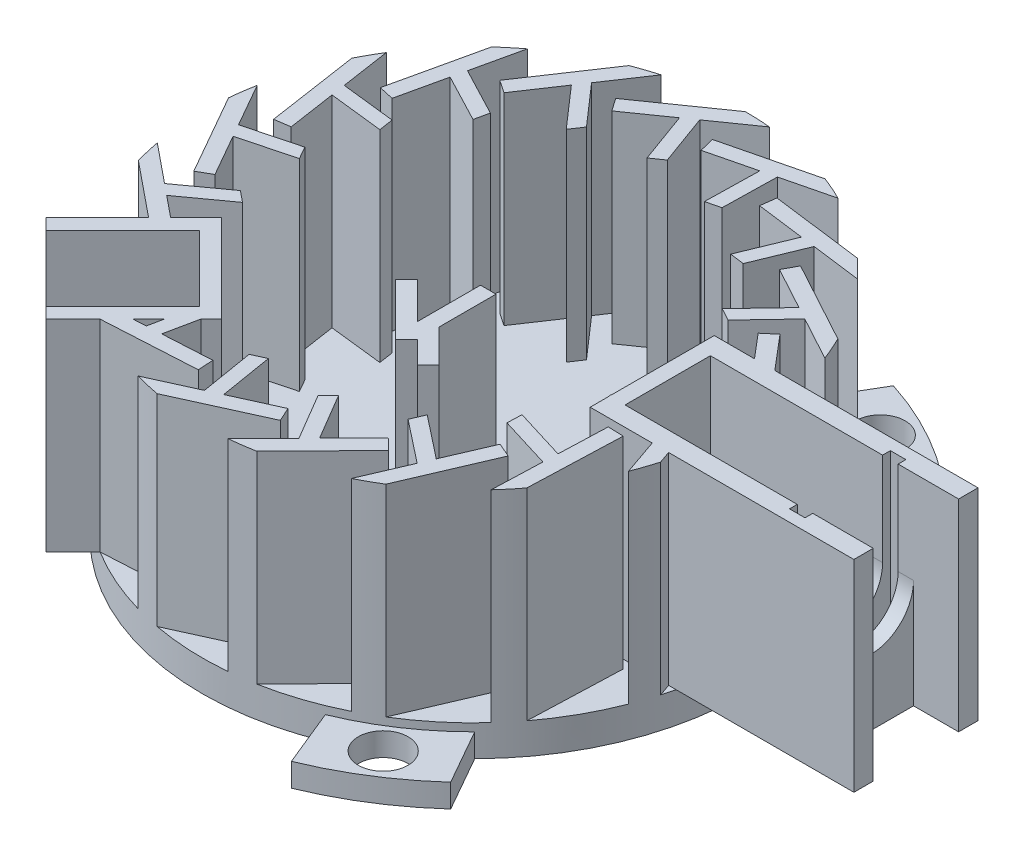
SolidWorks part; units mm, degrees
ref_plane "Front Plane" through (0, 0, 0) normal (0, 0, 1) x (1, 0, 0)
ref_plane "Top Plane" through (0, 0, 0) normal (0, 1, 0) x (1, 0, 0)
ref_plane "Right Plane" through (0, 0, 0) normal (1, 0, 0) x (0, 0, -1)
sketch "Sketch1" plane through (0, 0, 0) normal (0, 1, 0) x (1, 0, 0)
  circle A0 centre (0, 0) radius 17.5
  dimension "D1" = 35
extrude "Boss-Extrude1" add sketch "Sketch1" along normal blind 2
sketch "Sketch6" plane through (0, 2, 0) normal (0, 1, 0) x (1, 0, 0)
  line L1 (0, 17.5) -> (-4.9149, 14.0585)
  line L2 (-4.9149, 14.0585) -> (-4.3413, 13.2394)
  line L3 (-4.3413, 13.2394) -> (-1.7776, 15.0346)
  line L4 (-1.3536, 15.3315) -> (-0.3275, 12.5124) construction
  line L5 (-1.7776, 15.0346) -> (-0.5805, 11.7456)
  line L6 (-1.0084, 15.5731) -> (0.1886, 12.2842)
  line L7 (-0.5805, 11.7456) -> (0.1886, 12.2842)
  line L8 (-1.0084, 15.5731) -> (1.6342, 17.4235)
  line L9 (6.3217, 16.3183) -> (0.4955, 14.8847)
  line L10 (0.4955, 14.8847) -> (0.7344, 13.9136)
  line L11 (0.7344, 13.9136) -> (3.7736, 14.6614)
  line L12 (3.7736, 14.6614) -> (3.7017, 11.1622)
  line L13 (3.7017, 11.1622) -> (4.6135, 11.3865)
  line L14 (4.6853, 14.8858) -> (4.6135, 11.3865)
  line L15 (4.6853, 14.8858) -> (7.818, 15.6566)
  line L16 (11.7897, 12.9327) -> (5.839, 13.7005)
  line L17 (5.839, 13.7005) -> (5.711, 12.7088)
  line L18 (5.711, 12.7088) -> (8.8151, 12.3082)
  line L19 (8.8151, 12.3082) -> (7.484, 9.0712)
  line L20 (7.484, 9.0712) -> (8.4152, 8.951)
  line L21 (9.7463, 12.188) -> (8.4152, 8.951)
  line L22 (9.7463, 12.188) -> (12.9459, 11.7752)
  line L23 (15.6654, 7.8004) -> (10.3939, 10.6661)
  line L24 (10.3939, 10.6661) -> (9.9163, 9.7875)
  line L25 (9.9163, 9.7875) -> (12.666, 8.2927)
  line L26 (12.666, 8.2927) -> (10.2555, 5.7551)
  line L27 (10.2555, 5.7551) -> (11.0804, 5.3067)
  line L28 (13.491, 7.8442) -> (11.0804, 5.3067)
  line L29 (13.491, 7.8442) -> (16.3253, 6.3034)
  line L30 (17.4253, 1.6147) -> (13.5451, 6.1911)
  line L31 (13.5451, 6.1911) -> (12.7823, 5.5444)
  line L32 (12.7823, 5.5444) -> (14.8064, 3.1572)
  line L33 (14.8064, 3.1572) -> (11.642, 1.6618)
  line L34 (11.642, 1.6618) -> (12.2492, 0.9456)
  line L35 (15.4136, 2.441) -> (12.2492, 0.9456)
  line L36 (15.4136, 2.441) -> (17.5, -0.0196)
  line L37 (16.8319, -4.7891) -> (14.8669, 0.88)
  line L38 (14.8669, 0.88) -> (13.922, 0.5525)
  line L39 (13.922, 0.5525) -> (14.9471, -2.4047)
  line L40 (14.9471, -2.4047) -> (11.4561, -2.656)
  line L41 (11.4561, -2.656) -> (11.7636, -3.5432)
  line L42 (15.2546, -3.2919) -> (11.7636, -3.5432)
  line L43 (15.2546, -3.2919) -> (16.3112, -6.34)
  line L44 (13.9653, -10.5461) -> (14.1809, -4.55)
  line L45 (14.1809, -4.55) -> (13.1815, -4.5141)
  line L46 (13.1815, -4.5141) -> (13.0691, -7.6418)
  line L47 (13.0691, -7.6418) -> (9.723, -6.6151)
  line L48 (9.723, -6.6151) -> (9.6893, -7.5534)
  line L49 (13.0353, -8.5802) -> (9.6893, -7.5534)
  line L50 (13.0353, -8.5802) -> (12.9194, -11.8042)
  line L51 (9.2126, -14.8788) -> (11.5796, -9.3654)
  line L52 (11.5796, -9.3654) -> (10.6607, -8.9709)
  line L53 (10.6607, -8.9709) -> (9.426, -11.8469)
  line L54 (9.426, -11.8469) -> (6.6768, -9.6807)
  line L55 (6.6768, -9.6807) -> (6.3064, -10.5435)
  line L56 (9.0556, -12.7097) -> (6.3064, -10.5435)
  line L57 (9.0556, -12.7097) -> (7.7829, -15.6741)
  line L58 (3.2156, -17.202) -> (7.4145, -12.9161)
  line L59 (7.4145, -12.9161) -> (6.7001, -12.2162)
  line L60 (6.7001, -12.2162) -> (4.5099, -14.4519)
  line L61 (4.5099, -14.4519) -> (2.7289, -11.439)
  line L62 (2.7289, -11.439) -> (2.0718, -12.1097)
  line L63 (3.8528, -15.1227) -> (2.0718, -12.1097)
  line L64 (3.8528, -15.1227) -> (1.5952, -17.4271)
  line L65 (-3.2156, -17.202) -> (2.248, -14.7223)
  line L66 (2.248, -14.7223) -> (1.8347, -13.8117)
  line L67 (1.8347, -13.8117) -> (-1.0153, -15.1052)
  line L68 (-1.0153, -15.1052) -> (-1.5876, -11.6523)
  line L69 (-1.5876, -11.6523) -> (-2.4426, -12.0404)
  line L70 (-1.8703, -15.4933) -> (-2.4426, -12.0404)
  line L71 (-1.8703, -15.4933) -> (-4.808, -16.8266)
  line L72 (-9.2126, -14.8788) -> (-3.2221, -14.5402)
  line L73 (-3.2221, -14.5402) -> (-3.2786, -13.5418)
  line L74 (-3.2786, -13.5418) -> (-6.4033, -13.7184)
  line L75 (-6.4033, -13.7184) -> (-5.6897, -10.2919)
  line L76 (-5.6897, -10.2919) -> (-6.6272, -10.3449)
  line L77 (-7.3408, -13.7714) -> (-6.6272, -10.3449)
  line L78 (-7.3408, -13.7714) -> (-10.5618, -13.9535)
  line L79 (-13.9653, -10.5461) -> (-8.2571, -12.3943)
  line L80 (-8.2571, -12.3943) -> (-7.949, -11.443)
  line L81 (-7.949, -11.443) -> (-10.9266, -10.4789)
  line L82 (-10.9266, -10.4789) -> (-9.0234, -7.5416)
  line L83 (-9.0234, -7.5416) -> (-9.9167, -7.2523)
  line L84 (-11.8199, -10.1896) -> (-9.9167, -7.2523)
  line L85 (-11.8199, -10.1896) -> (-14.8891, -9.1959)
  line L86 (-16.8319, -4.7891) -> (-12.1768, -8.5746)
  line L87 (-12.1768, -8.5746) -> (-11.5459, -7.7987)
  line L88 (-11.5459, -7.7987) -> (-13.9742, -5.8241)
  line L89 (-13.9742, -5.8241) -> (-11.1384, -3.7727)
  line L90 (-11.1384, -3.7727) -> (-11.8669, -3.1803)
  line L91 (-14.7027, -5.2317) -> (-11.8669, -3.1803)
  line L92 (-14.7027, -5.2317) -> (-17.2056, -3.1963)
  line L93 (-17.4253, 1.6147) -> (-14.4521, -3.5968)
  line L94 (-14.4521, -3.5968) -> (-13.5835, -3.1012)
  line L95 (-13.5835, -3.1012) -> (-15.1344, -0.3828)
  line L96 (-15.1344, -0.3828) -> (-11.7491, 0.5057)
  line L97 (-11.7491, 0.5057) -> (-12.2144, 1.3213)
  line L98 (-15.5997, 0.4328) -> (-12.2144, 1.3213)
  line L99 (-15.5997, 0.4328) -> (-17.1984, 3.2349)
  line L100 (-15.6654, 7.8004) -> (-14.7755, 1.8668)
  line L101 (-14.7755, 1.8668) -> (-13.7865, 2.0151)
  line L102 (-13.7865, 2.0151) -> (-14.2507, 5.1103)
  line L103 (-14.2507, 5.1103) -> (-10.773, 4.7158)
  line L104 (-10.773, 4.7158) -> (-10.9123, 5.6444)
  line L105 (-14.39, 6.0388) -> (-10.9123, 5.6444)
  line L106 (-14.39, 6.0388) -> (-14.8685, 9.2292)
  line L107 (-11.7897, 12.9327) -> (-13.1033, 7.0782)
  line L108 (-13.1033, 7.0782) -> (-12.1276, 6.8593)
  line L109 (-12.1276, 6.8593) -> (-11.4424, 9.9131)
  line L110 (-11.4424, 9.9131) -> (-8.342, 8.289)
  line L111 (-8.342, 8.289) -> (-8.1364, 9.2052)
  line L112 (-11.2368, 10.8293) -> (-8.1364, 9.2052)
  line L113 (-11.2368, 10.8293) -> (-10.5304, 13.9771)
  line L114 (-6.3217, 16.3183) -> (-9.6616, 11.3337)
  line L115 (-9.6616, 11.3337) -> (-8.8308, 10.7771)
  line L116 (-8.8308, 10.7771) -> (-7.0886, 13.3772)
  line L117 (-7.0886, 13.3772) -> (-4.7843, 10.7428)
  line L118 (-4.7843, 10.7428) -> (-4.2617, 11.5228)
  line L119 (-6.566, 14.1572) -> (-4.2617, 11.5228)
  line L120 (-6.566, 14.1572) -> (-4.7702, 16.8373)
  circle A1 centre (0, 0) radius 17.5
  arc A2 (1.6342, 17.4235) -> (0, 17.5) centre (0, 0) ccw
  arc A3 (7.818, 15.6566) -> (6.3217, 16.3183) centre (0, 0) ccw
  arc A4 (12.9459, 11.7752) -> (11.7897, 12.9327) centre (0, 0) ccw
  arc A5 (16.3253, 6.3034) -> (15.6654, 7.8004) centre (0, 0) ccw
  arc A6 (17.5, -0.0196) -> (17.4253, 1.6147) centre (0, 0) ccw
  arc A7 (16.3112, -6.34) -> (16.8319, -4.7891) centre (0, 0) ccw
  arc A8 (12.9194, -11.8042) -> (13.9653, -10.5461) centre (0, 0) ccw
  arc A9 (7.7829, -15.6741) -> (9.2126, -14.8788) centre (0, 0) ccw
  arc A10 (1.5952, -17.4271) -> (3.2156, -17.202) centre (0, 0) ccw
  arc A11 (-4.808, -16.8266) -> (-3.2156, -17.202) centre (0, 0) ccw
  arc A12 (-10.5618, -13.9535) -> (-9.2126, -14.8788) centre (0, 0) ccw
  arc A13 (-14.8891, -9.1959) -> (-13.9653, -10.5461) centre (0, 0) ccw
  arc A14 (-17.2056, -3.1963) -> (-16.8319, -4.7891) centre (0, 0) ccw
  arc A15 (-17.1984, 3.2349) -> (-17.4253, 1.6147) centre (0, 0) ccw
  arc A16 (-14.8685, 9.2292) -> (-15.6654, 7.8004) centre (0, 0) ccw
  arc A17 (-10.5304, 13.9771) -> (-11.7897, 12.9327) centre (0, 0) ccw
  arc A18 (-4.7702, 16.8373) -> (-6.3217, 16.3183) centre (0, 0) ccw
  point P135 (0, 0)
  point P143 (0, 0)
  dimension "D2" = 6
  dimension "D3" = 3.5
  dimension "D4" = 1
  dimension "D5" = 3
  dimension "D6" = 75
  dimension "D7" = 0.5
  dimension "D8" = 3.5
  dimension "D9" = 17
  dimension "D1" = 0
extrude "Boss-Extrude2" add sketch "Sketch6" along normal blind 13
sketch "Sketch7" plane through (0, 2, 0) normal (0, 1, 0) x (1, 0, 0)
  line L0 (0, 0) -> (28.1783, 0) construction
  line L1 (11.5, 4) -> (28.5, 4)
  line L2 (11.5, 4) -> (11.5, -4)
  line L3 (11.5, -4) -> (28.5, -4)
  line L4 (28.5, 4) -> (28.5, -4)
  line L5 (17.5, 0) -> (17.5, -7.7892) construction
  arc A0 (17.5, -0.0196) -> (17.4253, 1.6147) centre (0, 0) ccw construction
  arc A3 (17.5, -0.0196) -> (17.5, 0) centre (0, 0) ccw
  dimension "D1" = 8
  dimension "D2" = 17
  dimension "D3" = 4
  dimension "D4" = 6
extrude "Boss-Extrude3" add sketch "Sketch7" along normal blind 13
sketch "Sketch8" plane through (0, 15, 0) normal (0, 1, 0) x (1, 0, 0)
  line L0 (11.5, 4) -> (11.5, -4) construction
  line L1 (12.5, 2.75) -> (27.5, 2.75)
  line L2 (12.5, 2.75) -> (12.5, -2.75)
  line L3 (12.5, -2.75) -> (27.5, -2.75)
  line L4 (27.5, 2.75) -> (27.5, -2.75)
  line L5 (0, 0) -> (29.6487, 0) construction
  dimension "D1" = 5.5
  dimension "D2" = 1
  dimension "D3" = 2.75
  dimension "D4" = 15
extrude "Cut-Extrude1" cut sketch "Sketch8" against normal blind 6
sketch "Sketch10" plane through (0, 9, 0) normal (0, 1, 0) x (1, 0, 0)
  line L0 (12.5, -2.75) -> (27.5, -2.75) construction
  line L1 (12.5, 2.75) -> (16, 2.75)
  line L2 (12.5, 2.75) -> (12.5, -2.75)
  line L3 (12.5, -2.75) -> (16, -2.75)
  line L4 (16, 2.75) -> (16, -2.75)
  dimension "D1" = 3.5
extrude "Cut-Extrude2" cut sketch "Sketch10" against normal blind 6
sketch "Sketch14" plane through (28.5, 0, 0) normal (1, 0, 0) x (0, 0, -1)
  line L0 (-2.75, 9) -> (2.75, 9) construction
  line L1 (4, 15) -> (-4, 15) construction
  line L2 (4, 15) -> (4, 2) construction
  line L3 (4, 2) -> (-4, 2) construction
  line L4 (-4, 15) -> (-4, 2) construction
  circle A0 centre (0, 9) radius 2.75
  dimension "D1" = 5.5
extrude "Cut-Extrude3" cut sketch "Sketch14" against normal blind 13 from surface at -1 contours A0 starting at face at (27.5, 12, 0)
sketch "Sketch15" plane through (0, 15, 0) normal (0, 1, 0) x (1, 0, 0)
  line L0 (12.5, -2.75) -> (27.5, -2.75) construction
  line L1 (27.5, 2.75) -> (25.5944, 2.75)
  line L2 (27.5, 2.75) -> (27.5, -2.75)
  line L3 (27.5, -2.75) -> (25.5944, -2.75)
  line L4 (25.5944, 2.75) -> (25.5944, -2.75)
  line L5 (27.5, 0) -> (24.81, 0) construction
  line L6 (25.5944, 1) -> (27.5, 1)
  line L7 (25.5944, 1) -> (25.5944, -1)
  line L8 (25.5944, -1) -> (27.5, -1)
  line L9 (27.5, 1) -> (27.5, -1)
  line M11 (12.5, 2.75) -> (27.5, 2.75)
  line M12 (27.5, 2.75) -> (27.5, -2.75)
  line M13 (27.5, -2.75) -> (12.5, -2.75)
  dimension "D1" = 1
  dimension "D2" = 1
extrude "Cut-Extrude4" cut sketch "Sketch15" against normal blind 13 contours L8 L4 M13 M12 | L4 L6 M12 M11
sketch "Sketch16" plane through (0, 15, 0) normal (0, 1, 0) x (1, 0, 0)
  line L0 (28.5, 4) -> (28.5, -4) construction
  line L1 (25.5944, 2.75) -> (28.5, 2.75)
  line L2 (25.5944, 2.75) -> (25.5944, -2.753)
  line L3 (25.5944, -2.753) -> (28.5, -2.753)
  line L4 (28.5, 2.75) -> (28.5, -2.753)
extrude "Cut-Extrude5" cut sketch "Sketch16" against normal blind 13
sketch "Sketch17" plane through (0, 15, 0) normal (0, 1, 0) x (1, 0, 0)
  line L0 (12.5, -2.75) -> (25.5944, -2.75) construction
  line L1 (16, 2.75) -> (23.6, 2.75)
  line L2 (16, 2.75) -> (16, -2.75)
  line L3 (16, -2.75) -> (23.6, -2.75)
  line L4 (23.6, 2.75) -> (23.6, -2.75)
  line L5 (23.6, 2.75) -> (24.2817, 2.75) construction
  line L6 (23.6, 3.25) -> (24.6, 3.25)
  line L7 (23.6, 3.25) -> (23.6, -3.25)
  line L8 (23.6, -3.25) -> (24.6, -3.25)
  line L9 (24.6, 3.25) -> (24.6, -3.25)
  line L10 (28.5, 2.75) -> (12.5, 2.75) construction
  line L11 (23.6, -2.75) -> (24.253, -2.75) construction
  line M11 (12.5, 2.75) -> (28.5, 2.75)
  line M30 (25.5944, -2.75) -> (12.5, -2.75)
  dimension "D1" = 7.6
  dimension "D2" = 0.5
  dimension "D3" = 6.5
  dimension "D4" = 1
extrude "Cut-Extrude6" cut sketch "Sketch17" against normal blind 10 contours L9 L6 L7 M11 | L9 L4 M11 M30 | L9 L7 L8 M30
sketch "Sketch18" plane through (12.5, 0, 0) normal (1, 0, 0) x (0, 0, -1)
  line L4 (2.75, 15) -> (-2.75, 15)
  line L5 (-2.75, 15) -> (-2.75, 3)
  line L6 (-2.75, 3) -> (2.75, 3)
  line L7 (2.75, 3) -> (2.75, 15)
  line L8 (2.75, 15) -> (-2.75, 15)
  line L9 (-2.75, 15) -> (-2.75, 3)
  line L10 (-2.75, 3) -> (2.75, 3)
  line L11 (2.75, 3) -> (2.75, 15)
  arc A0 (-2.75, 9) -> (2.75, 9) centre (0, 9) ccw construction
  arc A1 (-2.75, 9) -> (2.75, 9) centre (0, 9) ccw
  circle A2 centre (0, 9) radius 2
  dimension "D2" = 4
  dimension "D1" = 0
extrude "Cut-Extrude7" cut sketch "Sketch18" against normal blind 10 contours A2
sketch "Sketch20" plane through (0, 2, 0) normal (0, 1, 0) x (1, 0, 0)
  line L0 (16, 0) -> (-26.5681, 0) construction
  line L1 (16, 2.75) -> (16, -2.75) construction
  line L2 (0, 0) -> (-20.494, 20.494) construction
  line L3 (-28.2695, 3.5207) -> (-1.2716, -23.4772) construction
  line L4 (0, 0) -> (-20.8502, -20.8502) construction
  line L5 (-22.981, -17.3241) -> (-10.9602, -5.3033)
  line L6 (-5.3033, -10.9602) -> (-17.3241, -22.981)
  line L7 (-17.3241, -22.981) -> (-22.981, -17.3241)
  line L8 (-10.9602, -5.3033) -> (-5.3033, -10.9602)
  arc A0 (-16.8319, -4.7891) -> (-14.8891, -9.1959) centre (0, 0) ccw construction
  dimension "D1" = 135
  dimension "D2" = 4
  dimension "D3" = 4
  dimension "D4" = 6
  dimension "D5" = 17
extrude "Boss-Extrude4" add sketch "Sketch20" along normal blind 13
sketch "Sketch21" plane through (0, 15, 0) normal (0, 1, 0) x (1, 0, 0)
  line L0 (-10.9602, -6.7175) -> (-21.5668, -17.3241)
  line L1 (-21.5668, -17.3241) -> (-17.3241, -21.5668)
  line L2 (-17.3241, -21.5668) -> (-6.7175, -10.9602)
  line L3 (-6.7175, -10.9602) -> (-10.9602, -6.7175)
  line L4 (-5.9564, -10.307) -> (-10.9602, -5.3033) construction
  line L5 (-22.981, -17.3241) -> (-17.3241, -22.981) construction
  line L6 (-17.3241, -22.981) -> (-9.2184, -14.8752) construction
  line L7 (-14.8752, -9.2184) -> (-22.981, -17.3241) construction
  line L8 (-5.9564, -10.307) -> (-10.9602, -5.3033)
  line L9 (-22.981, -17.3241) -> (-17.3241, -22.981)
  line L10 (-17.3241, -22.981) -> (-9.2184, -14.8752)
  line L11 (-14.8752, -9.2184) -> (-22.981, -17.3241)
  dimension "D1" = 1
  dimension "D2" = 1
  dimension "D3" = 1
  dimension "D4" = 1
extrude "Cut-Extrude8" cut sketch "Sketch21" against normal blind 6 contours L2 L3 L0 L1
sketch "Sketch22" plane through (0, 9, 0) normal (0, 1, 0) x (1, 0, 0)
  line L0 (-10.9602, -6.7175) -> (-6.7175, -10.9602)
  line L1 (-6.7175, -10.9602) -> (-9.5459, -13.7886)
  line L2 (-17.3241, -21.5668) -> (-6.7175, -10.9602) construction
  line L3 (-9.5459, -13.7886) -> (-13.7886, -9.5459)
  line L4 (-10.9602, -6.7175) -> (-21.5668, -17.3241) construction
  line L5 (-13.7886, -9.5459) -> (-10.9602, -6.7175)
  dimension "D1" = 4
extrude "Cut-Extrude9" cut sketch "Sketch22" against normal blind 7
sketch "Sketch23" plane through (-11.6673, 0, 11.6673) normal (0.7071, 0, -0.7071) x (-0.7071, 0, -0.7071)
  line L0 (3, 9) -> (-3, 9) construction
  circle A0 centre (0, 9) radius 2.6
  dimension "D1" = 5.2
extrude "Cut-Extrude10" cut sketch "Sketch23" against normal blind 3
sketch "Sketch24" plane through (0, 15, 0) normal (0, 1, 0) x (1, 0, 0)
  line L0 (-22.981, -17.3241) -> (-16.617, -10.9602)
  line L1 (-14.8752, -9.2184) -> (-22.981, -17.3241) construction
  line L2 (-16.617, -10.9602) -> (-10.9602, -16.617)
  line L3 (-17.3241, -22.981) -> (-9.2184, -14.8752) construction
  line L4 (-10.9602, -16.617) -> (-17.3241, -22.981)
  line L5 (-17.3241, -22.981) -> (-22.981, -17.3241)
  line L6 (-15.6271, -11.9501) -> (-11.9501, -15.6271) construction
  dimension "D1" = 0
extrude "Cut-Extrude11" cut sketch "Sketch24" against normal blind 22
sketch "Sketch25" plane through (-13.7886, 0, 13.7886) normal (-0.7071, 0, 0.7071) x (0.7071, 0, 0.7071)
  arc A0 (-2.6, 9) -> (2.6, 9) centre (0, 9) ccw construction
  arc A1 (-2.6, 9) -> (2.6, 9) centre (0, 9) ccw
  circle A2 centre (0, 9) radius 2.6
  arc M6 (2.6, 9) -> (-2.6, 9) centre (0, 9) cw
extrude "Cut-Extrude12" cut sketch "Sketch25" against normal blind 17 contours A2 M6
sketch "Sketch26" plane through (0, 2, 0) normal (0, 1, 0) x (1, 0, 0)
  line L0 (-8.8388, -8.8388) -> (-13.7886, -13.7886) construction
  line L1 (-6.7175, -10.9602) -> (-10.9602, -6.7175) construction
  line L2 (-15.6271, -11.9501) -> (-11.9501, -15.6271) construction
  line L3 (-8.1317, -12.3744) -> (-12.3744, -8.1317) construction
  line L4 (-9.5459, -13.7886) -> (-6.7175, -10.9602) construction
  line L5 (-10.9602, -6.7175) -> (-13.7886, -9.5459) construction
  point P16 (0, 0)
sketch "Sketch27" plane through (0, 15, 0) normal (0, 1, 0) x (1, 0, 0)
  line L0 (-11.3137, -9.1924) -> (-10.9602, -8.8388)
  line L1 (-8.1317, -12.3744) -> (-12.3744, -8.1317) construction
  line L2 (-10.9602, -8.8388) -> (-8.8388, -10.9602)
  line L3 (-8.8388, -10.9602) -> (-9.5459, -11.6673)
  line L4 (-9.5459, -11.6673) -> (-11.6673, -9.5459)
  line L5 (-11.6673, -9.5459) -> (-11.3137, -9.1924)
  line L6 (-11.2189, -11.2189) -> (-9.4086, -9.4086) construction
  line L7 (-8.8388, -8.8388) -> (-13.7886, -13.7886) construction
  line L8 (-11.5867, -8.9194) -> (-8.7609, -11.7452) construction
  dimension "D1" = 3
  dimension "D2" = 0.5
  dimension "D3" = 0.5
  dimension "D4" = 1.5
extrude "Cut-Extrude15" cut sketch "Sketch27" against normal blind 22
sketch "Sketch28" plane through (0, 2, 0) normal (0, 1, 0) x (1, 0, 0)
  line L0 (-17.5, 0) -> (0, 0) construction
  line L1 (-13.7886, -13.7886) -> (-2.8382, -2.8382) construction
  line L2 (-1.9117, -3.145) -> (1.4471, -6.5038)
  line L3 (1.4471, -6.5038) -> (2.1542, -5.7966)
  line L7 (2.1542, -4.3824) -> (4.2755, -6.5038)
  line L8 (4.2755, -6.5038) -> (3.5684, -7.2109)
  line L9 (3.5684, -7.2109) -> (2.1542, -5.7966)
  line L10 (1.1542, -4.3824) -> (1.1542, -4.7966)
  line L12 (2.1542, -4.3824) -> (2.1542, -0.7233)
  line L14 (1.1542, -4.3824) -> (1.1542, -0.7233)
  line L15 (1.1542, -4.7966) -> (-1.2046, -2.4379)
  line L16 (1.1542, -0.7233) -> (2.1542, -0.7233)
  line L17 (2.162, 0) -> (47.4582, 0) construction
  line L18 (-1.9117, -3.145) -> (-1.2046, -2.4379)
  line L19 (-2.0807, -2.0807) -> (20.2405, 20.2405) construction
  arc A1 (-17.4253, 1.6147) -> (-17.2056, -3.1963) centre (0, 0) ccw construction
  dimension "D4" = 3
  dimension "D5" = 1
  dimension "D6" = 1
extrude "Boss-Extrude5" add sketch "Sketch28" along normal blind 13
sketch "Sketch29" plane through (0, 15, 0) normal (0, 1, 0) x (1, 0, 0)
  line L0 (-5.9564, -10.307) -> (-5.7383, -10.5252)
  line L1 (-5.9564, -10.307) -> (-5.6897, -10.2919)
  line L2 (-5.6897, -10.2919) -> (-5.7383, -10.5252)
extrude "Cut-Extrude16" cut sketch "Sketch29" against normal blind 13
sketch "Sketch30" plane through (0, 0, 0) normal (0, 1, 0) x (1, 0, 0)
  line L0 (8.8979, 14.5479) -> (11.8462, 18.8525) construction
  line L1 (9.2582, 20.7368) -> (5.9714, 15.9379) construction
  line L2 (4.4896, 16.9143) -> (6.5761, 20.4696)
  line L3 (10.7134, 13.8373) -> (13.1622, 17.0002)
  line L4 (12.4034, -12.3453) -> (14.4391, -15.9299)
  line L5 (6.6268, -16.1968) -> (8.1415, -19.8989)
  line L6 (-16.893, -4.569) -> (-21.0153, -4.5397)
  line L7 (-17.3402, 2.3594) -> (-21.3037, 2.8987)
  arc A0 (-21.3037, 2.8987) -> (-21.0153, -4.5397) centre (0, 0) ccw
  circle A1 centre (10.6021, -16.3958) radius 1.6
  arc A2 (-17.3402, 2.3594) -> (-16.893, -4.569) centre (0, 0) ccw
  circle A3 centre (8.8981, 17.3796) radius 1.6
  circle A4 centre (-19.5003, -0.9838) radius 1.6
  arc A5 (13.1622, 17.0002) -> (6.5761, 20.4696) centre (0, 0) ccw
  arc A6 (8.1415, -19.8989) -> (14.4391, -15.9299) centre (0, 0) ccw
  arc A7 (10.7134, 13.8373) -> (4.4896, 16.9143) centre (0, 0) ccw
  arc A8 (6.6268, -16.1968) -> (12.4034, -12.3453) centre (0, 0) ccw
  point P12 (0, 0)
  point P30 (0, 0)
  dimension "D1" = 43
  dimension "D2" = 35
  dimension "D3" = 3.2
  dimension "D5" = 3
  dimension "D4" = 3
extrude "Boss-Extrude6" add sketch "Sketch30" along normal blind 1.5 contours L4 A6 L5 A8 | L7 A0 L6 A2 | L2 A5 L3 A7
sketch "Sketch31" plane through (0, 2, 0) normal (0, 1, 0) x (1, 0, 0)
  circle A0 centre (8.9098, 17.2938) radius 1.6
  circle A1 centre (10.522, -16.363) radius 1.6
  circle A2 centre (-19.4318, -0.9308) radius 1.6
  point P8 (0, 0)
  dimension "D1" = 3.2
  dimension "D2" = 3
extrude "Cut-Extrude17" cut sketch "Sketch31" against normal blind 16.5
